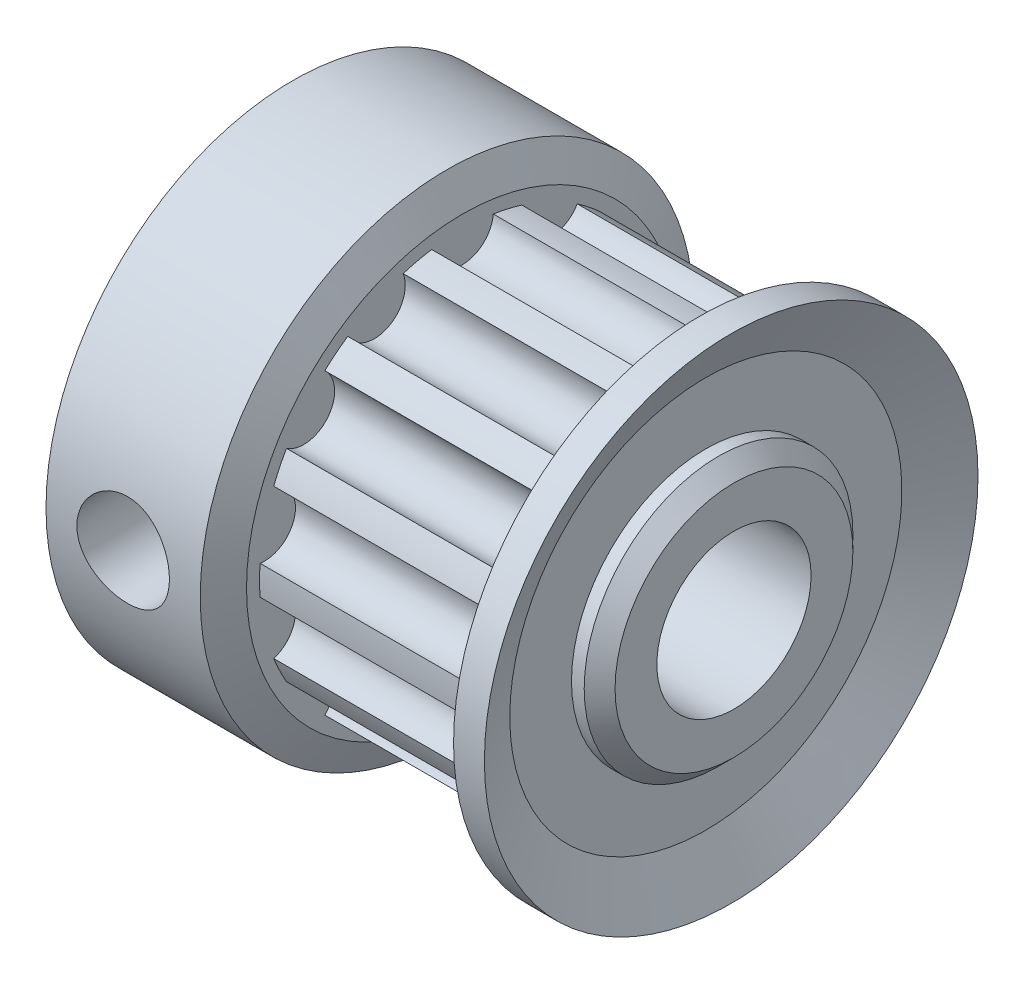
SolidWorks part; units mm, degrees
ref_plane "Front Plane" through (0, 0, 0) normal (0, 0, 1) x (1, 0, 0)
ref_plane "Top Plane" through (0, 0, 0) normal (0, 1, 0) x (1, 0, 0)
ref_plane "Right Plane" through (0, 0, 0) normal (1, 0, 0) x (0, 0, -1)
sketch "Sketch1" plane through (0, 0, 0) normal (0, 0, 1) x (1, 0, 0)
  line L0 (0, 7) -> (0, 0) construction
  line L1 (0, 0) -> (14.8, 0) construction
  line L2 (0, 7) -> (0, 3.9)
  line L3 (0.1, 3.8) -> (0.3, 3.8)
  line L4 (0.3, 3.8) -> (0, 3.5)
  line L5 (0, 3.5) -> (0, 0)
  line L6 (0, 0) -> (14.8, 0)
  line L7 (6, 6.5786) -> (13, 6.5786)
  line L8 (5.5, 8) -> (6, 7)
  line L9 (0, 7) -> (0.5, 8)
  line L10 (0.5, 8) -> (5.5, 8)
  line L11 (6, 7) -> (6, 6.5786)
  line L12 (13, 6.5786) -> (13.7107, 8)
  line L13 (13.7107, 8) -> (14.7107, 8)
  line L14 (14.7107, 8) -> (13.8878, 6.3543)
  line L15 (13.8878, 6.3543) -> (13.8878, 4.3543)
  line L16 (13.8878, 4.3543) -> (14.3, 4.3543)
  line L17 (14.8, 3.8543) -> (14.8, 0)
  line L19 (14.3, 4.3543) -> (14.8, 3.8543)
  arc A0 (0, 3.9) -> (0.1, 3.8) centre (0.1, 3.9) ccw
  point P12 (0, 3.8)
  point P19 (14.8, 4.3543)
  dimension "D12" = 0.1
  dimension "D1" = 14.8
  dimension "D2" = 7
  dimension "D3" = 5
  dimension "D4" = 0.5
  dimension "D5" = 1
  dimension "D6" = 0.5
  dimension "D7" = 1
  dimension "D8" = 8
  dimension "D9" = 3.2
  dimension "D10" = 0.3
  dimension "D11" = 0.3
  dimension "D13" = 1
  dimension "D14" = 1.84
  dimension "D15" = 2
  dimension "D16" = 8
revolve "Revolve1" add sketch "Sketch1" angle 360 about L6
sketch "Sketch2" plane through (14.8, 0, 0) normal (1, 0, 0) x (0, 0, -1)
  circle A0 centre (0, 0) radius 2.5
  dimension "D1" = 5
extrude "Cut-Extrude1" cut sketch "Sketch2" against normal through all
sketch "Sketch3" plane through (6, 0, 0) normal (1, 0, 0) x (0, 0, -1)
  line L0 (0, 0) -> (0, 6.5786) construction
  circle A9 centre (2.8544, 5.9272) radius 1
  circle A10 centre (0, 6.5786) radius 1
  circle A11 centre (5.1434, 4.1017) radius 1
  circle A12 centre (6.4137, 1.4639) radius 1
  circle A13 centre (6.4137, -1.4639) radius 1
  circle A14 centre (5.1434, -4.1017) radius 1
  circle A15 centre (2.8544, -5.9272) radius 1
  circle A16 centre (0, -6.5786) radius 1
  circle A17 centre (-2.8544, -5.9272) radius 1
  circle A18 centre (-5.1434, -4.1017) radius 1
  circle A19 centre (-6.4137, -1.4639) radius 1
  circle A20 centre (-6.4137, 1.4639) radius 1
  circle A21 centre (-5.1434, 4.1017) radius 1
  circle A22 centre (-2.8544, 5.9272) radius 1
  point P35 (0, 0)
  dimension "D1" = 2
  dimension "D2" = 14
extrude "Cut-Extrude2" cut sketch "Sketch3" along normal blind 7
sketch "Sketch4" plane through (0, 0, 0) normal (0, 0, 1) x (1, 0, 0)
  circle A0 centre (3, 0) radius 1.5
  dimension "D1" = 3
  dimension "D2" = 3
extrude "Cut-Extrude3" cut sketch "Sketch4" along normal through all
